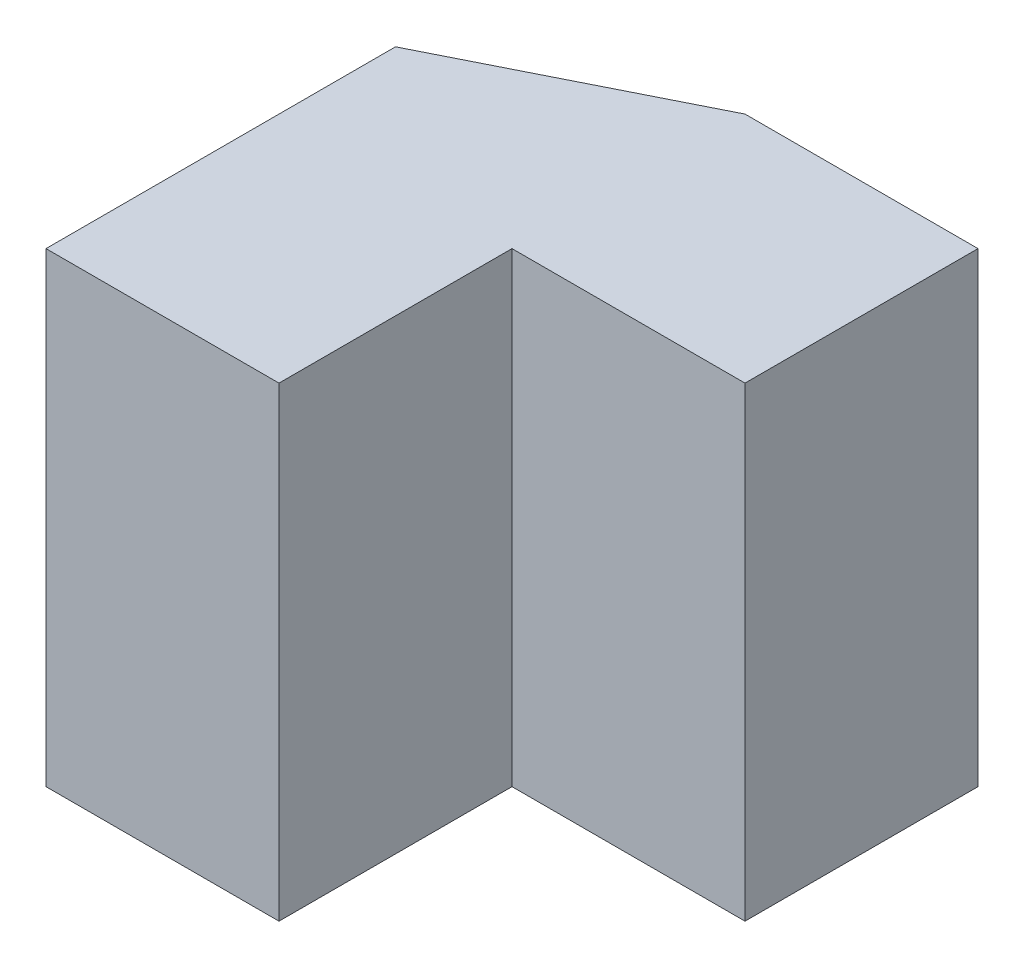
SolidWorks part; units mm, degrees
ref_plane "Front Plane" through (0, 0, 0) normal (0, 0, 1) x (1, 0, 0)
ref_plane "Top Plane" through (0, 0, 0) normal (0, 1, 0) x (1, 0, 0)
ref_plane "Right Plane" through (0, 0, 0) normal (1, 0, 0) x (0, 0, -1)
sketch "Sketch1" plane through (0, 0, 0) normal (0, 0, 1) x (1, 0, 0)
  line L1 (0, 0) -> (20, 0)
  line L2 (0, 0) -> (0, 20)
  line L3 (0, 20) -> (20, 20)
  line L4 (20, 0) -> (20, 20)
  dimension "D1" = 20
  dimension "D2" = 20
extrude "Boss-Extrude1" add sketch "Sketch1" along normal blind 20
sketch "Sketch2" plane through (0, 20, 0) normal (0, 1, 0) x (1, 0, 0)
  line L1 (20, -20) -> (10, -20)
  line L2 (20, -20) -> (20, -10)
  line L3 (20, -10) -> (10, -10)
  line L4 (10, -20) -> (10, -10)
  dimension "D1" = 10
  dimension "D2" = 10
extrude "Cut-Extrude1" cut sketch "Sketch2" against normal blind 20
sketch "Sketch3" plane through (0, 20, 0) normal (0, 1, 0) x (1, 0, 0)
  line L0 (0, 0) -> (10, 0)
  line L1 (20, 0) -> (0, 0) construction
  line L2 (10, 0) -> (0, -5)
  line L3 (0, -20) -> (0, 0) construction
  line L4 (0, -5) -> (0, 0)
  dimension "D1" = 10
  dimension "D2" = 5
extrude "Cut-Extrude2" cut sketch "Sketch3" against normal blind 20
